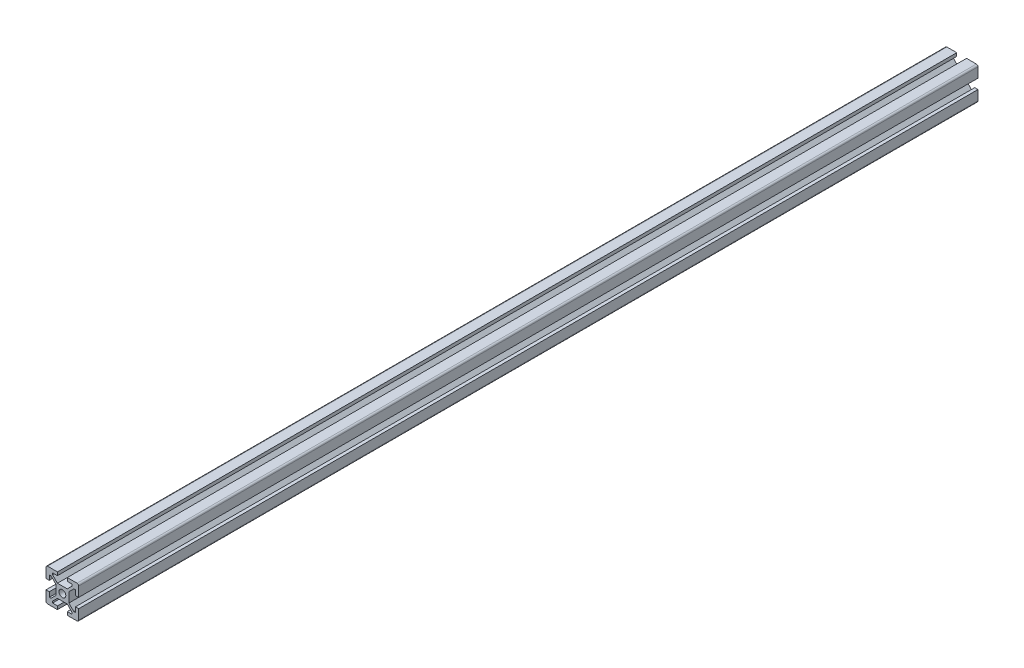
SolidWorks part; units mm, degrees
material "6063-O, Barra estrusa (SS)"
ref_plane "Piano frontale" through (0, 0, 0) normal (0, 0, 1) x (1, 0, 0)
ref_plane "Piano superiore" through (0, 0, 0) normal (0, 1, 0) x (1, 0, 0)
ref_plane "Piano destro" through (0, 0, 0) normal (1, 0, 0) x (0, 0, -1)
other "Lunghezza"
sketch "Schizzo1" plane through (0, 0, 0) normal (0, 0, 1) x (1, 0, 0)
  line L0 (-6, 8) -> (6, 8) construction
  line L1 (10, 3) -> (10, 10)
  line L2 (8, 3) -> (10, 3)
  line L3 (10, 10) -> (3, 10)
  line L4 (8, 6) -> (8, 3)
  line L5 (10, -10) -> (-10, 10) construction
  line L6 (10, 10) -> (-10, -10) construction
  line L7 (0, 23.5419) -> (0, -15.5419) construction
  line L8 (-13.4777, 0) -> (13.4408, 0) construction
  line L9 (-3, 4) -> (3, 4) construction
  line L10 (3, 4) -> (9, 10) construction
  line L11 (6, 11.4787) -> (6, 3.0667) construction
  line L12 (-6, 11.4787) -> (-6, 3.0667) construction
  line L13 (-3, 4) -> (-9, 10) construction
  line L14 (-3, 4) -> (-6, 7)
  line L15 (-6, 7) -> (-6, 8)
  line L16 (-6, 8) -> (-3, 8)
  line L17 (6, 8) -> (6, 7)
  line L18 (6, 7) -> (3, 4)
  line L19 (3, 4) -> (-3, 4)
  line L20 (-3, 8) -> (-3, 10)
  line L21 (6, 8) -> (3, 8)
  line L22 (3, 8) -> (3, 10)
  line L23 (-3, 10) -> (-10, 10)
  line L24 (7, 6) -> (8, 6)
  line L25 (4, 3) -> (7, 6)
  line L26 (4, -3) -> (4, 3)
  line L27 (7, -6) -> (4, -3)
  line L28 (8, -6) -> (7, -6)
  line L29 (8, -6) -> (8, -3)
  line L30 (8, -3) -> (10, -3)
  line L31 (10, -10) -> (10, -3)
  line L32 (3, -10) -> (10, -10)
  line L33 (3, -8) -> (3, -10)
  line L34 (6, -8) -> (3, -8)
  line L35 (6, -7) -> (6, -8)
  line L36 (3, -4) -> (6, -7)
  line L37 (-3, -4) -> (3, -4)
  line L38 (-6, -7) -> (-3, -4)
  line L39 (-6, -8) -> (-6, -7)
  line L40 (-6, -8) -> (-3, -8)
  line L41 (-3, -8) -> (-3, -10)
  line L42 (-10, -10) -> (-3, -10)
  line L43 (-10, -3) -> (-10, -10)
  line L44 (-8, -3) -> (-10, -3)
  line L45 (-8, -6) -> (-8, -3)
  line L46 (-7, -6) -> (-8, -6)
  line L47 (-4, -3) -> (-7, -6)
  line L48 (-4, 3) -> (-4, -3)
  line L49 (-7, 6) -> (-4, 3)
  line L50 (-8, 6) -> (-7, 6)
  line L51 (-8, 6) -> (-8, 3)
  line L52 (-8, 3) -> (-10, 3)
  line L53 (-10, 10) -> (-10, 3)
  circle A0 centre (0, 0) radius 2.1
  point P0 (0, 0)
  point P10 (0, 8)
  point P17 (0, 4)
  point P69 (0, 0)
  dimension "D6" = 4.2
  dimension "D1" = 20
  dimension "D2" = 10
  dimension "D3" = 2
  dimension "D4" = 12
  dimension "D5" = 4
  dimension "D7" = 4
  dimension "D8" = 6
  dimension "D9" = 6
  dimension "D10" = 3
  dimension "D11" = 4
extrude "Estrusione-Estrusione1" add sketch "Schizzo1" along normal blind 550
fillet "Raccordo1" radius 1 4 edges at (-10, -10, 275) (10, -10, 275) (-10, 10, 275) (10, 10, 275)
